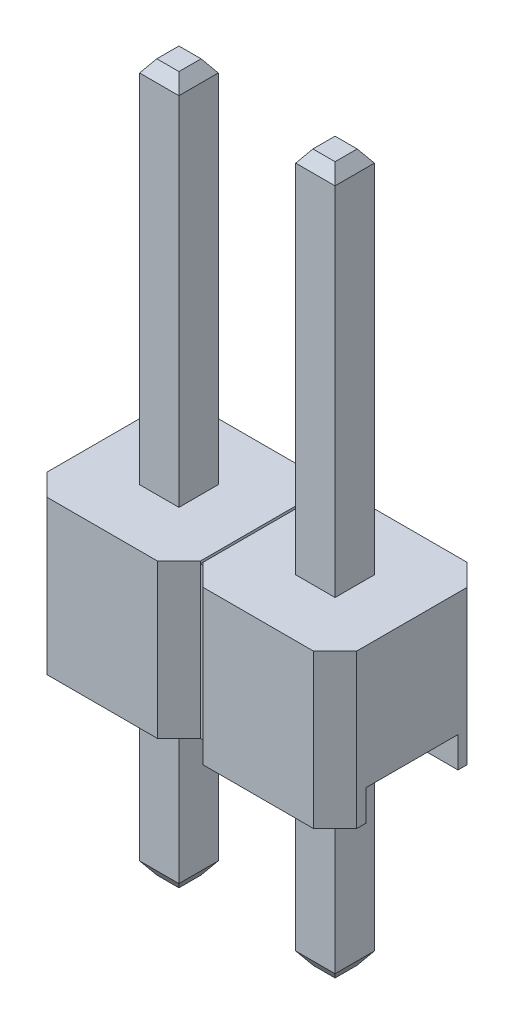
SolidWorks part; units mm, degrees
ref_plane "Front Plane" through (0, 0, 0) normal (0, 0, 1) x (1, 0, 0)
ref_plane "Top Plane" through (0, 0, 0) normal (0, 1, 0) x (1, 0, 0)
ref_plane "Right Plane" through (0, 0, 0) normal (1, 0, 0) x (0, 0, -1)
sketch "Sketch1" plane through (0, 0, 0) normal (0, 1, 0) x (1, 0, 0)
  line L0 (0, 2.15) -> (0.35, 2.5)
  line L1 (0.35, 0) -> (2.15, 0)
  line L2 (0, 0.35) -> (0, 2.15)
  line L3 (0.35, 2.5) -> (2.15, 2.5)
  line L5 (2.15, 2.5) -> (2.5, 2.15)
  line L6 (0, 0.35) -> (0.35, 0)
  line L7 (2.15, 0) -> (2.5, 0.35)
  line L9 (2.54, 0.35) -> (2.89, 0)
  line L10 (2.54, 2.15) -> (2.89, 2.5)
  line L11 (2.89, 0) -> (4.69, 0)
  line L12 (4.69, 0) -> (5.04, 0.35)
  line L14 (4.69, 2.5) -> (5.04, 2.15)
  line L15 (2.89, 2.5) -> (4.69, 2.5)
  line L64 (0, 0.35) -> (2.54, 0.35) construction
  line L65 (2.5, 2.15) -> (2.54, 2.15)
  line L68 (2.54, 0.35) -> (2.54, 2.15) [skipped]
  line L69 (5.08, 0.35) -> (5.08, 2.15) [skipped]
  line L71 (7.62, 0.35) -> (7.62, 2.15) [skipped]
  line L73 (10.16, 0.35) -> (10.16, 2.15) [skipped]
  line L75 (12.7, 0.35) -> (12.7, 2.15) [skipped]
  line L76 (15.24, 0.35) -> (15.24, 2.15) [skipped]
  line L77 (17.78, 0.35) -> (17.78, 2.15) [skipped]
  line L84 (2.54, 0.35) -> (2.5, 0.35)
  line L86 (18.13, 0) -> (19.93, 0) [skipped]
  line L87 (18.13, 2.5) -> (19.93, 2.5) [skipped]
  line L88 (15.24, 2.15) -> (15.59, 2.5) [skipped]
  line L89 (14.85, 2.5) -> (15.2, 2.15) [skipped]
  line L90 (12.7, 2.15) -> (13.05, 2.5) [skipped]
  line L91 (12.31, 2.5) -> (12.66, 2.15) [skipped]
  line L92 (10.16, 2.15) -> (10.51, 2.5) [skipped]
  line L93 (9.77, 2.5) -> (10.12, 2.15) [skipped]
  line L94 (7.62, 2.15) -> (7.97, 2.5) [skipped]
  line L95 (7.23, 2.5) -> (7.58, 2.15) [skipped]
  line L96 (5.43, 2.5) -> (7.23, 2.5) [skipped]
  line L97 (5.08, 2.15) -> (5.43, 2.5) [skipped]
  line L98 (7.97, 2.5) -> (9.77, 2.5) [skipped]
  line L99 (10.51, 2.5) -> (12.31, 2.5) [skipped]
  line L100 (15.59, 2.5) -> (17.39, 2.5) [skipped]
  line L101 (17.78, 2.15) -> (18.13, 2.5) [skipped]
  line L102 (17.39, 2.5) -> (17.74, 2.15) [skipped]
  line L103 (13.05, 2.5) -> (14.85, 2.5) [skipped]
  line L104 (19.93, 2.5) -> (20.28, 2.15) [skipped]
  line L105 (19.93, 0) -> (20.28, 0.35) [skipped]
  line L106 (17.78, 0.35) -> (18.13, 0) [skipped]
  line L107 (15.59, 0) -> (17.39, 0) [skipped]
  line L108 (17.39, 0) -> (17.74, 0.35) [skipped]
  line L109 (15.24, 0.35) -> (15.59, 0) [skipped]
  line L110 (14.85, 0) -> (15.2, 0.35) [skipped]
  line L111 (13.05, 0) -> (14.85, 0) [skipped]
  line L112 (12.7, 0.35) -> (13.05, 0) [skipped]
  line L113 (12.31, 0) -> (12.66, 0.35) [skipped]
  line L114 (9.77, 0) -> (10.12, 0.35) [skipped]
  line L115 (10.16, 0.35) -> (10.51, 0) [skipped]
  line L116 (10.51, 0) -> (12.31, 0) [skipped]
  line L117 (5.08, 0.35) -> (5.43, 0) [skipped]
  line L118 (5.43, 0) -> (7.23, 0) [skipped]
  line L119 (7.23, 0) -> (7.58, 0.35) [skipped]
  line L120 (7.62, 0.35) -> (7.97, 0) [skipped]
  line L121 (7.97, 0) -> (9.77, 0) [skipped]
  line L122 (5.04, 2.15) -> (5.04, 0.35)
  point P0 (0, 0)
  point P1 (2.5, 2.5)
  point P2 (0, 2.5)
  point P3 (2.5, 0)
  dimension "D2" = 2.5
  dimension "D3" = 2.5
  dimension "D4" = 2.54
extrude "Boss-Extrude1" add sketch "Sketch1" along normal blind 2.5
sketch "Sketch2" plane through (0, 0, 0) normal (0, -1, 0) x (1, 0, 0)
  line L0 (0, -1.25) -> (5.04, -1.25) construction
  line L3 (0, -2.15) -> (0, -0.35) construction
  line L8 (5.04, -0.35) -> (5.04, -2.15) construction
  line L10 (0, -2) -> (5.04, -2)
  line L11 (0, -2) -> (0, -0.5)
  line L12 (0, -0.5) -> (5.04, -0.5)
  line L13 (5.04, -2) -> (5.04, -0.5)
  line L14 (0, -2) -> (5.04, -0.5) construction
  line L15 (0, -0.5) -> (5.04, -2) construction
  point P6 (2.52, -1.25)
  dimension "D1" = 1.5
extrude "Cut-Extrude1" cut sketch "Sketch2" against normal blind 0.5
sketch "Sketch4" plane through (0, 2.5, 0) normal (0, 1, 0) x (1, 0, 0)
  line L0 (5.08, 2.15) -> (5.08, 0.35)
  line L1 (2.5, 2.15) -> (2.54, 2.15)
  line L2 (2.5, 2.15) -> (2.5, 0.35)
  line L3 (2.5, 0.35) -> (2.54, 0.35)
  line L4 (2.54, 2.15) -> (2.54, 0.35)
  line L5 (5.04, 2.15) -> (5.04, 0.35)
  line L6 (5.04, 2.15) -> (5.08, 2.15)
  line L7 (5.04, 0.35) -> (5.08, 0.35)
  line L8 (7.62, 2.15) -> (7.62, 0.35)
  line L9 (7.58, 2.15) -> (7.58, 0.35)
  line L10 (7.58, 2.15) -> (7.62, 2.15)
  line L11 (7.58, 0.35) -> (7.62, 0.35)
  line L12 (10.16, 2.15) -> (10.16, 0.35)
  line L13 (10.12, 2.15) -> (10.12, 0.35)
  line L14 (10.12, 2.15) -> (10.16, 2.15)
  line L15 (10.12, 0.35) -> (10.16, 0.35)
  line L16 (12.7, 2.15) -> (12.7, 0.35)
  line L17 (12.66, 2.15) -> (12.66, 0.35)
  line L18 (12.66, 2.15) -> (12.7, 2.15)
  line L19 (12.66, 0.35) -> (12.7, 0.35)
  line L20 (15.24, 2.15) -> (15.24, 0.35)
  line L21 (15.2, 2.15) -> (15.2, 0.35)
  line L22 (15.2, 2.15) -> (15.24, 2.15)
  line L23 (15.2, 0.35) -> (15.24, 0.35)
  line L24 (17.78, 2.15) -> (17.78, 0.35)
  line L25 (17.74, 2.15) -> (17.74, 0.35)
  line L26 (17.74, 2.15) -> (17.78, 2.15)
  line L27 (17.74, 0.35) -> (17.78, 0.35)
  line L28 (2.54, 2.15) -> (5.08, 2.15) construction
  dimension "D1" = 2.54
extrude "Cut-Extrude2" cut sketch "Sketch4" against normal blind 0.04
sketch "Sketch3" plane through (0, 2.5, 0) normal (0, 1, 0) x (1, 0, 0)
  line L0 (1.25, 2.5) -> (1.25, 0) construction
  line L1 (2.15, 2.5) -> (0.35, 2.5) construction
  line L2 (0.35, 0) -> (2.15, 0) construction
  line L3 (0, 1.25) -> (1.25, 1.25) construction
  line L4 (0, 2.15) -> (0, 0.35) construction
  line L6 (0.93, 0.93) -> (1.57, 0.93)
  line L7 (0.93, 0.93) -> (0.93, 1.57)
  line L8 (0.93, 1.57) -> (1.57, 1.57)
  line L9 (1.57, 0.93) -> (1.57, 1.57)
  line L10 (0.93, 0.93) -> (1.57, 1.57) construction
  line L11 (0.93, 1.57) -> (1.57, 0.93) construction
  dimension "D1" = 0.64
extrude "Boss-Extrude2" add sketch "Sketch3" along normal blind 6 and the other way blind 5.5
chamfer "Chamfer1" distance 0.2 angle 35 8 edges at (1.25, -3, -1.57) (0.93, -3, -1.25) (1.25, -3, -0.93) (1.57, -3, -1.25) (1.25, 8.5, -0.93) (0.93, 8.5, -1.25) (1.25, 8.5, -1.57) (1.57, 8.5, -1.25)
pattern_linear "LPattern1" count 2 spacing 2.54 along (1, 0, 0) of "Chamfer1", "Boss-Extrude2"
